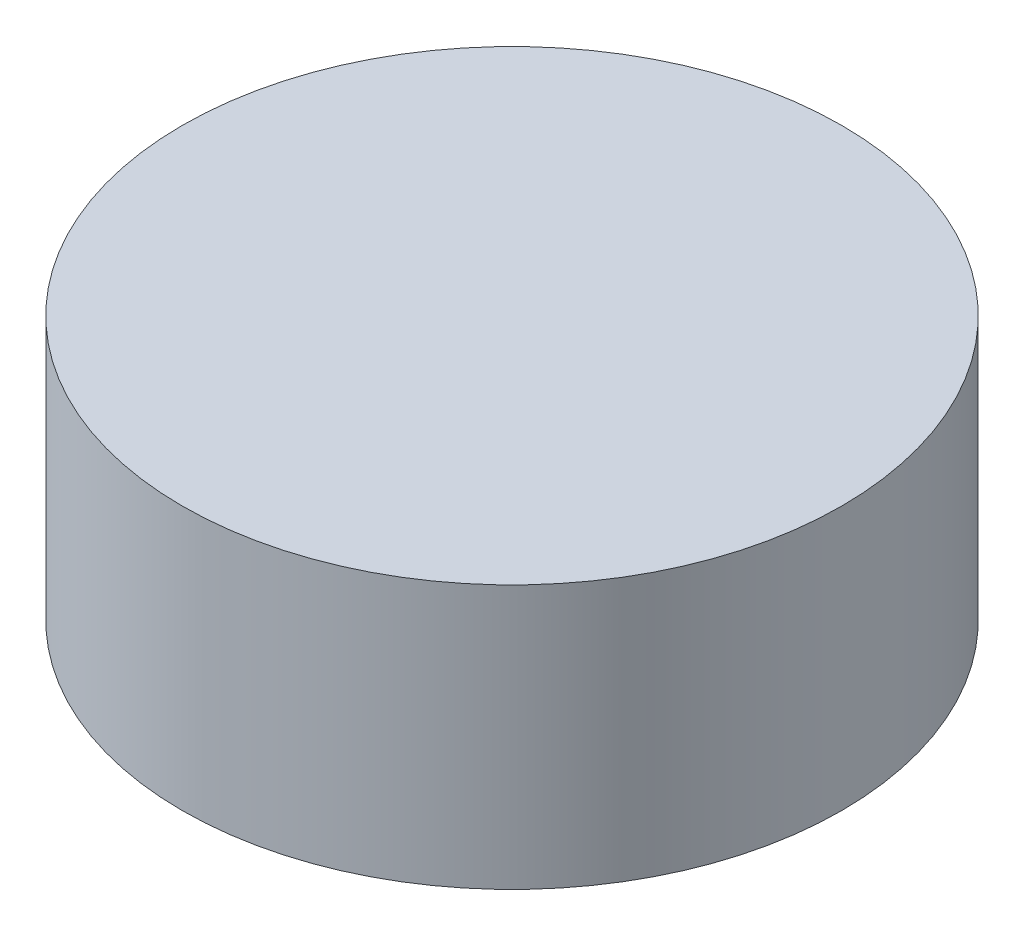
SolidWorks part; units mm, degrees
ref_plane "Front Plane" through (0, 0, 0) normal (0, 0, 1) x (1, 0, 0)
ref_plane "Top Plane" through (0, 0, 0) normal (0, 1, 0) x (1, 0, 0)
ref_plane "Right Plane" through (0, 0, 0) normal (1, 0, 0) x (0, 0, -1)
sketch "Sketch1" plane through (0, 0, 0) normal (0, 1, 0) x (1, 0, 0)
  circle A0 centre (0, 0) radius 12.5
  dimension "D1" = 25
extrude "Boss-Extrude1" add sketch "Sketch1" along normal blind 10
